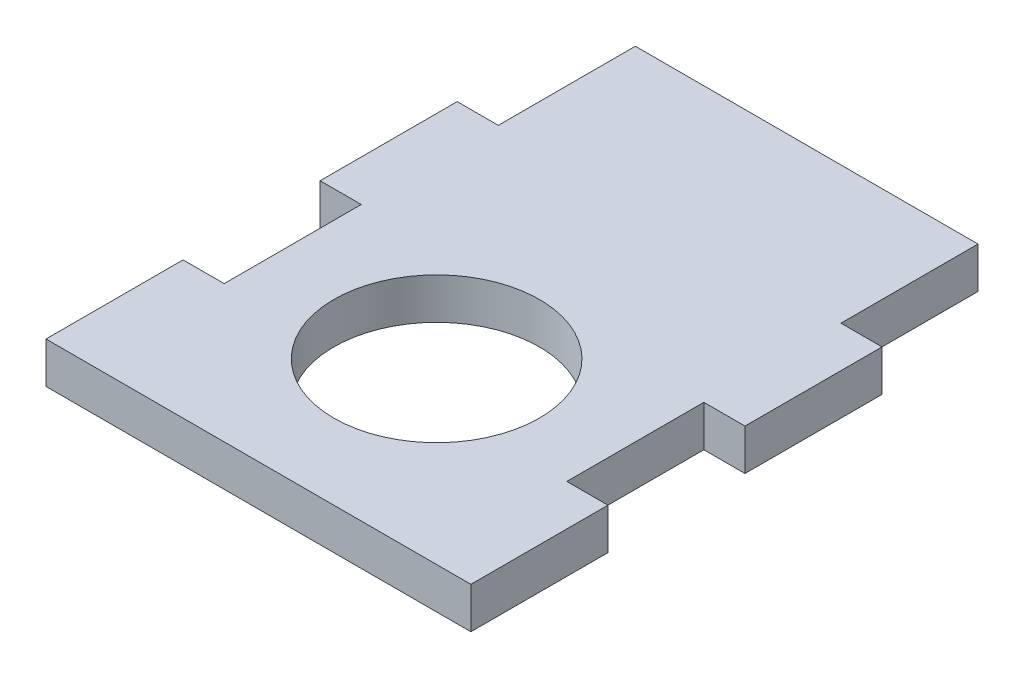
SolidWorks part; units mm, degrees
material "PC High Viscosity"
ref_plane "Front Plane" through (0, 0, 0) normal (0, 0, 1) x (1, 0, 0)
ref_plane "Top Plane" through (0, 0, 0) normal (0, 1, 0) x (1, 0, 0)
ref_plane "Right Plane" through (0, 0, 0) normal (1, 0, 0) x (0, 0, -1)
sketch "Sketch1" plane through (0, 0, 0) normal (0, 1, 0) x (1, 0, 0)
  line L1 (12.5, -20) -> (-12.5, -20)
  line L2 (12.5, -20) -> (12.5, 20)
  line L3 (12.5, 20) -> (-12.5, 20)
  line L4 (-12.5, -20) -> (-12.5, 20)
  line L5 (12.5, -20) -> (-12.5, 20) construction
  line L6 (12.5, 20) -> (-12.5, -20) construction
  point P0 (0, 0)
  dimension "D1" = 25
  dimension "D2" = 40
extrude "Boss-Extrude1" add sketch "Sketch1" along normal blind 3
sketch "Sketch2" plane through (0, 3, 0) normal (0, 1, 0) x (1, 0, 0)
  line L0 (12.5, -20) -> (12.5, 20) construction
  line L1 (12.5, -10) -> (15.5, -10)
  line L2 (12.5, -10) -> (12.5, -20)
  line L3 (12.5, -20) -> (15.5, -20)
  line L4 (15.5, -10) -> (15.5, -20)
  line L5 (12.5, 0) -> (12.5, -10) construction
  line L6 (12.5, 0) -> (15.5, 0)
  line L7 (12.5, 0) -> (12.5, 10)
  line L8 (12.5, 10) -> (15.5, 10)
  line L9 (15.5, 0) -> (15.5, 10)
  line L10 (-12.5, -20) -> (12.5, -20) construction
  line L11 (0, -20) -> (0, 20) construction
  line L12 (12.5, 20) -> (-12.5, 20) construction
  line L13 (-15.5, -10) -> (-15.5, -20)
  line L14 (-12.5, -20) -> (-15.5, -20)
  line L15 (-12.5, -10) -> (-12.5, -20)
  line L16 (-12.5, -10) -> (-15.5, -10)
  line L17 (-15.5, 0) -> (-15.5, 10)
  line L18 (-12.5, 10) -> (-15.5, 10)
  line L19 (-12.5, 0) -> (-12.5, 10)
  line L20 (-12.5, 0) -> (-15.5, 0)
  dimension "D1" = 10
  dimension "D2" = 3
extrude "Boss-Extrude2" add sketch "Sketch2" against normal up to surface (3 mm away) up to face at (0, 0, 0)
sketch "Sketch3" plane through (0, 3, 0) normal (0, 1, 0) x (1, 0, 0)
  line L0 (-15.5, -20) -> (15.5, -20) construction
  circle A0 centre (0, -7) radius 7.5
  point P4 (0, 0)
  dimension "D1" = 15
  dimension "D2" = 13
extrude "Cut-Extrude1" cut sketch "Sketch3" against normal through all
equation "\"pulley_pitch_diam\"= 12.73mm"
equation "\"pulley_total_width\"= 16mm"
equation "\"pulley_total_diam\"= 16mm"
equation "\"belt_width\"= 6mm"
equation "\"material_thickness\"= 3mm"
equation "\"shaft_diam\"= 8mm"
equation "\"bearing_od\"= 22mm"
equation "\"bearing_thickness\"= 7mm"
equation "\"D1@Boss-Extrude1\"=\"material_thickness\""
equation "\"D2@Sketch2\"=\"material_thickness\""
